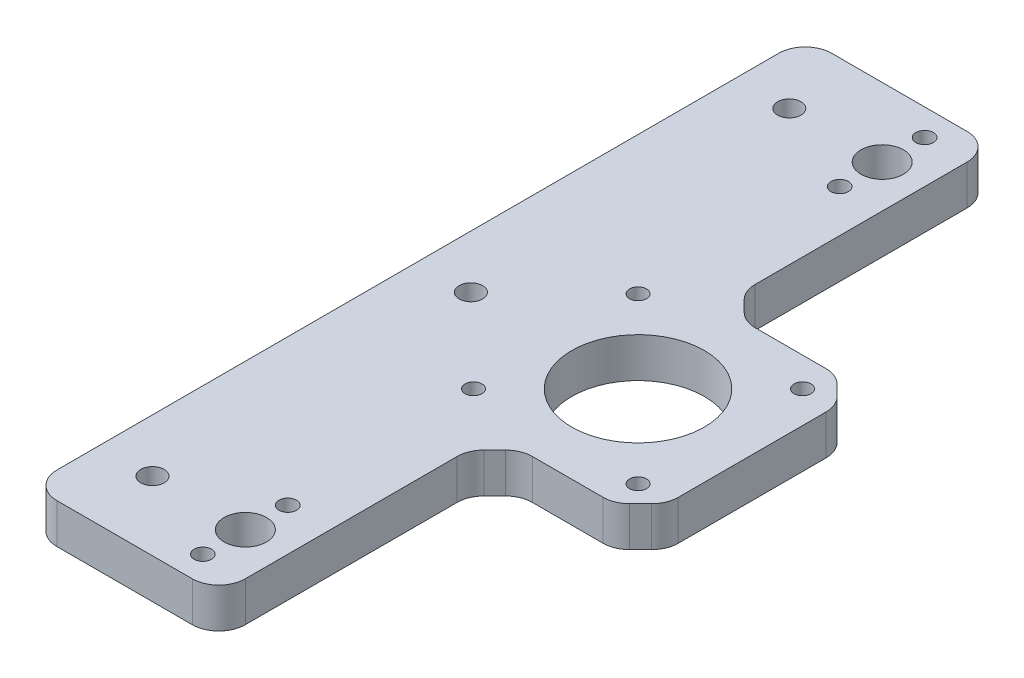
SolidWorks part; units mm, degrees
ref_plane "Front Plane" through (0, 0, 0) normal (0, 0, 1) x (1, 0, 0)
ref_plane "Top Plane" through (0, 0, 0) normal (0, 1, 0) x (1, 0, 0)
ref_plane "Right Plane" through (0, 0, 0) normal (1, 0, 0) x (0, 0, -1)
ref_plane "Plane1" through (0, 3.75, 0) normal (0, 1, 0) x (1, 0, 0)
sketch "Sketch1" plane through (0, 3.75, 0) normal (0, 1, 0) x (1, 0, 0)
  line L0 (34.0355, 17.4645) -> (31.9645, 19.5355)
  line L1 (28.4289, 21) -> (15.0711, 21)
  line L2 (11.5355, 22.4645) -> (9.4645, 24.5355)
  line L3 (8, 28.0711) -> (8, 68)
  line L4 (3, 73) -> (-22.5, 73)
  line L5 (-27.5, 68) -> (-27.5, -68)
  line L6 (-22.5, -73) -> (3, -73)
  line L7 (8, -68) -> (8, -28.0711)
  line L8 (9.4645, -24.5355) -> (11.5355, -22.4645)
  line L9 (15.0711, -21) -> (28.4289, -21)
  line L10 (31.9645, -19.5355) -> (34.0355, -17.4645)
  line L11 (35.5, -13.9289) -> (35.5, 13.9289)
  circle A0 centre (0, -68) radius 1.65
  circle A1 centre (0, -52) radius 1.65
  circle A2 centre (0, 68) radius 1.65
  circle A3 centre (0, 52) radius 1.65
  circle A4 centre (29.5, 15.5) radius 1.6
  circle A5 centre (-1.5, 15.5) radius 1.6
  circle A6 centre (-1.5, -15.5) radius 1.6
  circle A7 centre (29.5, -15.5) radius 1.6
  circle A8 centre (14, 0) radius 12.5
  circle A9 centre (-17.5, 0) radius 2.2
  circle A10 centre (0, -60) radius 4
  arc A11 (31.9645, 19.5355) -> (28.4289, 21) centre (28.4289, 16) ccw
  arc A12 (15.0711, 21) -> (11.5355, 22.4645) centre (15.0711, 26) cw
  arc A13 (9.4645, 24.5355) -> (8, 28.0711) centre (13, 28.0711) cw
  arc A14 (8, 68) -> (3, 73) centre (3, 68) ccw
  arc A15 (-22.5, 73) -> (-27.5, 68) centre (-22.5, 68) ccw
  arc A16 (-27.5, -68) -> (-22.5, -73) centre (-22.5, -68) ccw
  arc A17 (3, -73) -> (8, -68) centre (3, -68) ccw
  arc A18 (8, -28.0711) -> (9.4645, -24.5355) centre (13, -28.0711) cw
  arc A19 (11.5355, -22.4645) -> (15.0711, -21) centre (15.0711, -26) cw
  arc A20 (28.4289, -21) -> (31.9645, -19.5355) centre (28.4289, -16) ccw
  arc A21 (34.0355, -17.4645) -> (35.5, -13.9289) centre (30.5, -13.9289) ccw
  arc A22 (35.5, 13.9289) -> (34.0355, 17.4645) centre (30.5, 13.9289) ccw
  circle A23 centre (0, 60) radius 4
  circle A24 centre (-17.5, 60) radius 2.2
  circle A25 centre (-17.5, -60) radius 2.2
extrude "Boss-Extrude1" add sketch "Sketch1" against normal blind 7.5
